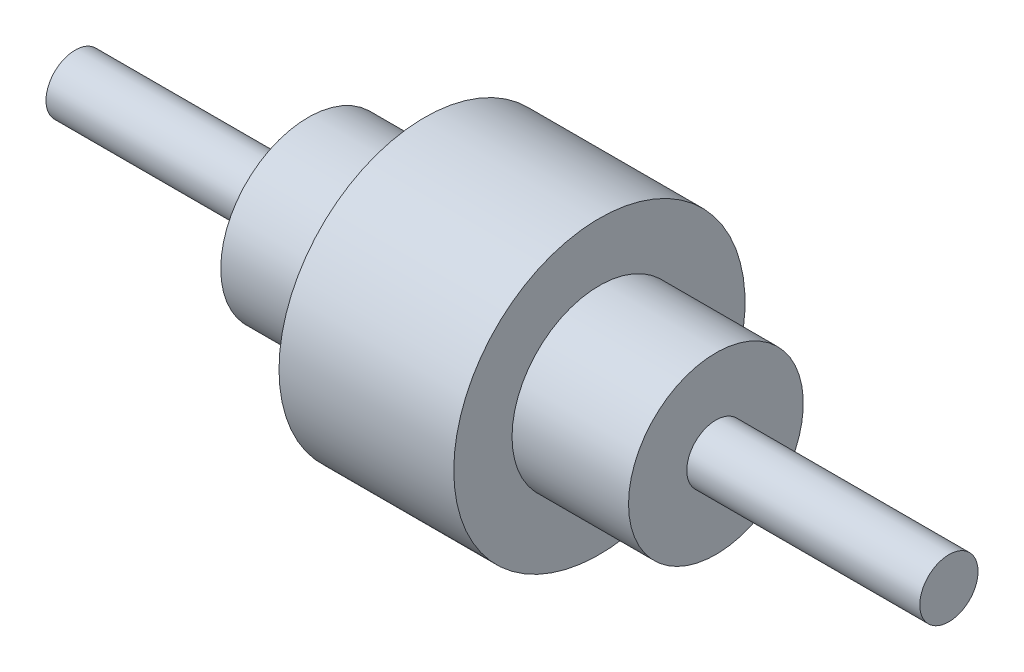
SolidWorks part; units mm, degrees
ref_plane "Front Plane" through (0, 0, 0) normal (0, 0, 1) x (1, 0, 0)
ref_plane "Top Plane" through (0, 0, 0) normal (0, 1, 0) x (1, 0, 0)
ref_plane "Right Plane" through (0, 0, 0) normal (1, 0, 0) x (0, 0, -1)
sketch "Sketch1" plane through (0, 0, 0) normal (0, 1, 0) x (1, 0, 0)
  line L0 (0, 0) -> (111.8072, 0) construction
  line L1 (0, 0) -> (0, 10)
  line L2 (0, 10) -> (80, 10)
  line L3 (80, 10) -> (80, 30)
  line L4 (80, 30) -> (120, 30)
  line L5 (120, 30) -> (120, 50)
  line L6 (120, 50) -> (180, 50)
  line L7 (180, 50) -> (180, 30)
  line L8 (180, 30) -> (220, 30)
  line L9 (220, 30) -> (220, 10)
  line L10 (220, 10) -> (300, 10)
  line L11 (300, 10) -> (300, 0)
  line L12 (111.8072, 0) -> (243.3012, 0) construction
  line L13 (0, 0) -> (300, 0)
  dimension "D1" = 20
  dimension "D2" = 60
  dimension "D3" = 100
  dimension "D4" = 80
  dimension "D5" = 40
  dimension "D6" = 60
revolve "Revolve1" add sketch "Sketch1" angle 360 about L13
